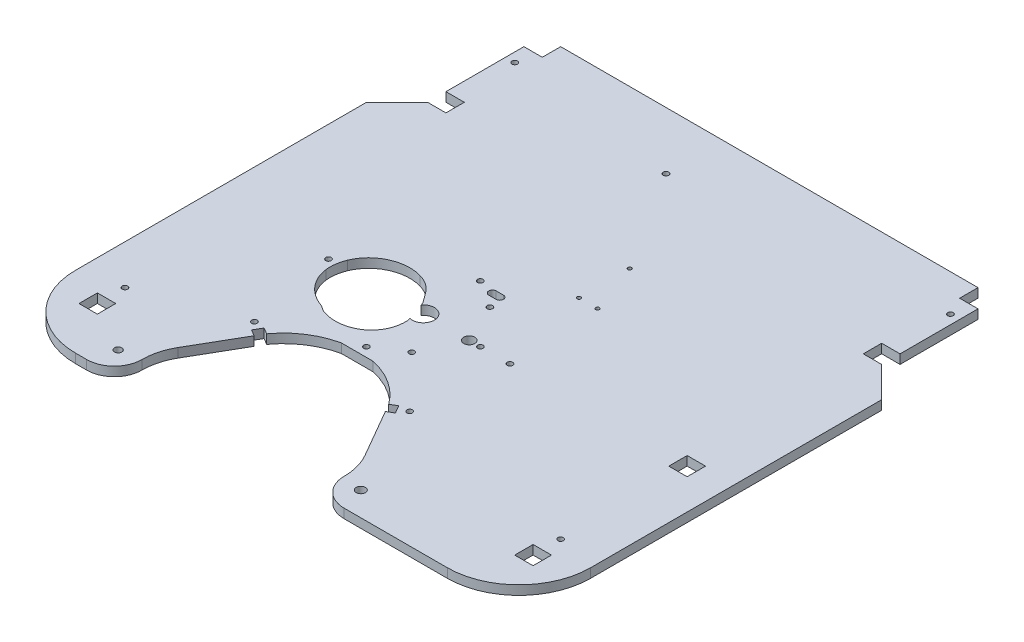
SolidWorks part; units mm, degrees
material "ABS PC"
ref_plane "Plan de face" through (0, 0, 0) normal (0, 0, 1) x (1, 0, 0)
ref_plane "Plan de dessus" through (0, 0, 0) normal (0, 1, 0) x (1, 0, 0)
ref_plane "Plan de droite" through (0, 0, 0) normal (1, 0, 0) x (0, 0, -1)
sketch "Esquisse1" plane through (0, 0, 0) normal (0, 1, 0) x (1, 0, 0)
  line L1 (-140.1, 31.2) -> (140.1, 31.2)
  line L2 (-140.1, 31.2) -> (-140.1, -245.0829)
  line L3 (-140.1, -245.0829) -> (140.1, -245.0829)
  line L4 (140.1, 31.2) -> (140.1, -245.0829)
  line L5 (45, -245.0829) -> (50, -245.0829) construction
  line L6 (-114.5, 31.2) -> (114.5, 31.2) construction
  line L7 (140.1, -4) -> (140.1, 4) construction
  line L8 (-140.1, 4) -> (-140.1, -4) construction
extrude "Boss.-Extru.1" add sketch "Esquisse1" along normal blind 5
sketch "Esquisse2" plane through (0, 0, 0) normal (0, 1, 0) x (1, 0, 0)
  line L3 (-58.1815, -184) -> (-61.6457, -182)
  line L4 (-61.6457, -182) -> (-64.1457, -186.3301)
  line L5 (-64.1457, -186.3301) -> (-60.6815, -188.3301)
  line L7 (-25, -132) -> (-25, -245.0829) construction
  line L8 (-58.1815, -184) -> (-60.6815, -188.3301) construction
  line L9 (-62.6323, -132) -> (62.6323, -132) construction
  line L10 (-25, -62.6323) -> (-25, 62.6323) construction
  line L11 (-60.6815, -188.3301) -> (-75.8539, -214.6094)
  line L13 (-58.1815, -184) -> (-54.7174, -186) construction
  line L14 (-25, -168.25) -> (-25, -231.25) construction
  line L16 (140.1, -245.0829) -> (-157.7205, -245.0829) construction
  line L17 (-140.1, -245.0829) -> (140.1, -245.0829) construction
  line L18 (8.1815, -184) -> (4.7174, -186) construction
  line L20 (8.1815, -184) -> (10.6815, -188.3301) construction
  line L21 (10.6815, -188.3301) -> (25.8539, -214.6094)
  line L22 (14.1457, -186.3301) -> (10.6815, -188.3301)
  line L23 (11.6457, -182) -> (14.1457, -186.3301)
  line L24 (8.1815, -184) -> (11.6457, -182)
  line L25 (-62.8957, -184.1651) -> (-67.2258, -181.6651) construction
  line L26 (-95, -245.0829) -> (45, -245.0829)
  arc A0 (-95, -245.0829) -> (-86.2863, -217.8734) centre (-95, -230.0829) ccw construction
  arc A1 (8.1815, -184) -> (-58.1815, -184) centre (-25, -208.0829) ccw
  arc A2 (-95, -245.0829) -> (-80, -230.0829) centre (-95, -230.0829) ccw
  arc A4 (-80, -230.0829) -> (-75.8539, -214.6094) centre (-49.0531, -230.0829) cw
  arc A5 (30, -230.0829) -> (25.8539, -214.6094) centre (-0.9469, -230.0829) ccw
  arc A6 (45, -245.0829) -> (30, -230.0829) centre (45, -230.0829) cw
  circle A8 centre (-67.2258, -181.6651) radius 1.5
  circle A10 centre (17.2258, -181.6651) radius 1.5
  dimension "D4" = 41
  dimension "D8" = 5
  dimension "D9" = 3
  dimension "D1" = 4
  dimension "D2" = 52
  dimension "D3" = 37
  dimension "D5" = 90
  dimension "D6" = 5
  dimension "D7" = 30
extrude "Enlèv. mat.-Extru.2" cut sketch "Esquisse2" along normal through all
sketch "Esquisse3" plane through (0, 5, 0) normal (0, 1, 0) x (1, 0, 0)
  line L0 (-30.2198, -127.0596) -> (-26.1089, -139.1328)
  spline S0 degree 3 poles (-37.7914, -122.1402) (-38.0734, -121.8243) (-38.3657, -121.5165) (-38.9965, -120.9381) (-39.3221, -120.6716) (-39.9982, -120.1678) (-40.3476, -119.9323) (-41.0674, -119.4915) (-41.4393, -119.2855) (-41.8168, -119.0963) knots 0 0 0 0 0.25 0.25 0.5 0.5 0.75 0.75 1 1 1 1 construction
  spline S1 degree 3 poles (-32.1541, -129.7487) (-32.3725, -129.4202) (-32.6019, -129.0988) (-33.0628, -128.4574) (-33.2929, -128.1364) (-33.9829, -127.1734) (-34.442, -126.5306) (-35.3645, -125.2486) (-35.8282, -124.6096) (-36.7788, -123.3501) (-37.2654, -122.7294) (-37.7914, -122.1402) knots 0 0 0 0 0.125 0.125 0.25 0.25 0.5 0.5 0.75 0.75 1 1 1 1 construction
  spline S2 degree 3 poles (-35.6619, -154.1946) (-35.0242, -153.7971) (-34.4156, -153.3543) (-33.5487, -152.619) (-33.2665, -152.3609) (-32.7231, -151.8244) (-32.4631, -151.5476) (-31.717, -150.6924) (-31.2669, -150.0877) (-30.6603, -149.1305) (-30.4697, -148.8029) (-30.1129, -148.13) (-29.9465, -147.7839) (-29.4899, -146.7378) (-29.243, -146.0234) (-28.8562, -144.563) (-28.7157, -143.8147) (-28.4532, -141.5381) (-28.491, -140.0256) (-28.7111, -138.5175) knots 0 0 0 0 0.125 0.125 0.1875 0.1875 0.25 0.25 0.375 0.375 0.4375 0.4375 0.5 0.5 0.625 0.625 0.75 0.75 1 1 1 1 construction
  spline S3 degree 3 poles (-35.6619, -154.1946) (-36.3253, -154.608) (-37.0218, -154.968) (-38.4509, -155.5833) (-39.1871, -155.8402) (-40.6929, -156.2533) (-41.4552, -156.4075) (-42.998, -156.615) (-43.7804, -156.6676) (-46.0993, -156.6733) (-47.6259, -156.4799) (-49.5088, -155.9804) (-49.8836, -155.8673) (-50.622, -155.6166) (-50.9867, -155.4786) (-51.7066, -155.1765) (-52.0616, -155.0123) (-52.5826, -154.748) (-52.7564, -154.66) (-53.0886, -154.4564) (-53.2465, -154.3401) (-53.4028, -154.2206) knots 0 0 0 0 0.125 0.125 0.25 0.25 0.375 0.375 0.5 0.5 0.75 0.75 0.8125 0.8125 0.875 0.875 0.9375 0.9375 0.96875 0.96875 1 1 1 1 construction
  spline S4 degree 3 poles (-41.8168, -119.0963) (-42.9717, -118.5173) (-44.1778, -118.0898) (-46.0518, -117.6406) (-46.691, -117.5235) (-47.9689, -117.3572) (-48.6085, -117.3074) (-49.8889, -117.2725) (-50.5296, -117.2869) (-51.8124, -117.3808) (-52.4575, -117.4608) (-54.3583, -117.7944) (-55.5875, -118.1406) (-57.3737, -118.8468) (-57.9613, -119.1147) (-59.1074, -119.714) (-59.6598, -120.0407) (-61.253, -121.1053) (-62.2339, -121.9217) (-63.3433, -123.0959) (-63.5595, -123.3389) (-63.9727, -123.8343) (-64.1705, -124.0875) (-64.7392, -124.8624) (-65.0859, -125.3992) (-65.725, -126.5066) (-66.0166, -127.0778) (-66.4118, -127.9607) (-66.5364, -128.2602) (-66.7677, -128.8619) (-66.8752, -129.1647) (-67.3727, -130.6881) (-67.6417, -131.9376) (-67.7975, -133.5423) (-67.8198, -133.8663) (-67.8456, -134.511) (-67.8492, -134.8322) (-67.832, -135.7928) (-67.7828, -136.429) (-67.6138, -137.6932) (-67.494, -138.3213) (-67.1803, -139.5691) (-66.9857, -140.1898) (-66.3106, -141.9951) (-65.7352, -143.1386) (-64.7029, -144.7728) (-64.3296, -145.3033) (-63.5406, -146.3156) (-63.1238, -146.8009) (-62.2475, -147.7313) (-61.7884, -148.177) (-60.8134, -149.015) (-60.2997, -149.4102) (-59.6532, -149.8941) (-59.524, -149.9912) (-59.2621, -150.18) (-59.1281, -150.2696) (-58.7233, -150.5349) (-58.4482, -150.704) (-57.6091, -151.1904) (-57.0301, -151.4842) (-56.1848, -151.9623) (-55.907, -152.1283) (-55.4954, -152.386) (-55.361, -152.4765) (-55.1045, -152.6783) (-54.9822, -152.7884) (-54.7446, -153.015) (-54.6281, -153.1308) (-54.3929, -153.36) (-54.2744, -153.4736) (-53.9142, -153.8089) (-53.6638, -154.0209) (-53.4028, -154.2206) knots 0 0 0 0 0.0625 0.0625 0.09375 0.09375 0.125 0.125 0.15625 0.15625 0.1875 0.1875 0.25 0.25 0.28125 0.28125 0.3125 0.3125 0.375 0.375 0.390625 0.390625 0.40625 0.40625 0.4375 0.4375 0.46875 0.46875 0.484375 0.484375 0.5 0.5 0.5625 0.5625 0.578125 0.578125 0.59375 0.59375 0.625 0.625 0.65625 0.65625 0.6875 0.6875 0.75 0.75 0.78125 0.78125 0.8125 0.8125 0.84375 0.84375 0.875 0.875 0.882813 0.882813 0.890625 0.890625 0.90625 0.90625 0.9375 0.9375 0.953125 0.953125 0.960938 0.960938 0.96875 0.96875 0.976563 0.976563 0.984375 0.984375 1 1 1 1 construction
  spline S30 degree 3 poles (-26.1089, -139.1328) (-25.957, -141.5638) (-26.2233, -144.068) (-26.9566, -146.3908) knots 0 0 0 0 1 1 1 1
  spline S31 degree 3 poles (-26.9566, -146.3908) (-27.2228, -147.2342) (-27.8831, -148.8893) (-29.2029, -151.171) (-30.8763, -153.2749) (-32.1537, -154.4712) (-32.834, -155.0244) knots 0 0 0 0 0.25 0.5 0.75 1 1 1 1
  spline S32 degree 3 poles (-32.834, -155.0244) (-34.0816, -156.0391) (-36.8741, -157.7375) (-39.9456, -158.6891) (-41.5144, -158.9883) knots 0 0 0 0 0.5 1 1 1 1
  spline S33 degree 3 poles (-41.5144, -158.9883) (-44.1178, -159.4848) (-46.8613, -159.4832) (-49.4654, -158.9908) knots 0 0 0 0 1 1 1 1
  spline S34 degree 3 poles (-49.4654, -158.9908) (-49.952, -158.8988) (-50.9201, -158.6805) (-51.9843, -158.3611) (-52.6895, -158.1153) (-53.0279, -157.9903) (-53.4112, -157.8436) (-53.8185, -157.6386) (-54.1411, -157.4539) (-54.4726, -157.2537) (-54.8017, -157.0368) (-54.9983, -156.9002) (-55.0989, -156.8301) knots 0 0 0 0 0.25 0.5 0.5625 0.625 0.6875 0.75 0.8125 0.875 0.9375 1 1 1 1
  spline S35 degree 3 poles (-55.0989, -156.8301) (-55.3218, -156.6748) (-55.8004, -156.3308) (-56.3372, -156.039) (-57.1153, -155.7047) (-58.1073, -155.2831) (-59.4212, -154.7248) (-60.6952, -154.0815) (-61.7162, -153.4751) (-62.6513, -152.8651) (-64.3061, -151.7169) (-66.4424, -149.811) (-68.6708, -147.1371) (-71.0288, -143.199) (-72.0496, -139.8117) (-72.3207, -137.531) knots 0 0 0 0 0.03125 0.0625 0.09375 0.125 0.1875 0.25 0.28125 0.3125 0.375 0.5 0.625 0.75 1 1 1 1
  spline S36 degree 3 poles (-72.3207, -137.531) (-72.524, -135.8208) (-72.4832, -132.3293) (-71.5647, -128.9796) (-70.9127, -127.3896) knots 0 0 0 0 0.5 1 1 1 1
  spline S37 degree 3 poles (-70.9127, -127.3896) (-70.401, -126.1419) (-69.1411, -123.7476) (-66.5657, -120.5334) (-63.4815, -117.9312) (-59.9208, -115.9009) (-56.1194, -114.5638) (-52.0895, -113.8994) (-48.0382, -113.9466) (-45.3685, -114.4522) (-44.0724, -114.8246) knots 0 0 0 0 0.125 0.25 0.375 0.5 0.625 0.75 0.875 1 1 1 1
  spline S38 degree 3 poles (-44.0724, -114.8246) (-43.1335, -115.0943) (-41.3015, -115.7539) (-39.094, -116.9388) (-37.4723, -118.0859) (-36.3006, -119.1013) (-35.2972, -120.193) (-34.6853, -120.94) (-34.3845, -121.3211) knots 0 0 0 0 0.25 0.5 0.625 0.75 0.875 1 1 1 1
  spline S39 degree 3 poles (-34.3845, -121.3211) (-33.6538, -122.2469) (-32.5988, -123.6857) (-31.2416, -125.568) (-30.5443, -126.5566) (-30.2198, -127.0596) knots 0 0 0 0 0.5 0.75 1 1 1 1
  spline S40 degree 3 poles (-544.0684, -2053.4709) (-13.3203, -329.9447) (2.5957, -129.3013) (-46.0518, -117.6406) (-46.691, -117.5235) (-47.9689, -117.3572) (-48.6085, -117.3074) (-49.8889, -117.2725) (-50.5296, -117.2869) (-51.8124, -117.3808) (-52.4575, -117.4608) (-54.3583, -117.7944) (-55.5875, -118.1406) (-57.3737, -118.8468) (-57.9613, -119.1147) (-59.1074, -119.714) (-59.6598, -120.0407) (-61.253, -121.1053) (-62.2339, -121.9217) (-63.3433, -123.0959) (-63.5595, -123.3389) (-63.9727, -123.8343) (-64.1705, -124.0875) (-64.7392, -124.8624) (-65.0859, -125.3992) (-65.725, -126.5066) (-66.0166, -127.0778) (-66.4118, -127.9607) (-66.5364, -128.2602) (-66.7677, -128.8619) (-66.8752, -129.1647) (-67.3727, -130.6881) (-67.6417, -131.9376) (-67.7975, -133.5423) (-67.8198, -133.8663) (-67.8456, -134.511) (-67.8492, -134.8322) (-67.832, -135.7928) (-67.7828, -136.429) (-67.6138, -137.6932) (-67.494, -138.3213) (-67.1803, -139.5691) (-66.9857, -140.1898) (-66.3106, -141.9951) (-65.7352, -143.1386) (-64.7029, -144.7728) (-64.3296, -145.3033) (-63.5406, -146.3156) (-63.1238, -146.8009) (-62.2475, -147.7313) (-61.7884, -148.177) (-60.8134, -149.015) (-60.2997, -149.4102) (-59.6532, -149.8941) (-59.524, -149.9912) (-59.2621, -150.18) (-59.1281, -150.2696) (-58.7233, -150.5349) (-58.4482, -150.704) (-57.6091, -151.1904) (-57.0301, -151.4842) (-56.1848, -151.9623) (-55.907, -152.1283) (-55.4954, -152.386) (-55.361, -152.4765) (-55.1045, -152.6783) (-54.9822, -152.7884) (-54.7446, -153.015) (-54.6281, -153.1308) (-54.3929, -153.36) (-54.2744, -153.4736) (-26.8241, -179.0197) (131.7308, -54.8381) (1346.14, 1273.1767) knots -2.339844 -2.339844 -2.339844 -2.339844 0.0625 0.0625 0.09375 0.09375 0.125 0.125 0.15625 0.15625 0.1875 0.1875 0.25 0.25 0.28125 0.28125 0.3125 0.3125 0.375 0.375 0.390625 0.390625 0.40625 0.40625 0.4375 0.4375 0.46875 0.46875 0.484375 0.484375 0.5 0.5 0.5625 0.5625 0.578125 0.578125 0.59375 0.59375 0.625 0.625 0.65625 0.65625 0.6875 0.6875 0.75 0.75 0.78125 0.78125 0.8125 0.8125 0.84375 0.84375 0.875 0.875 0.882813 0.882813 0.890625 0.890625 0.90625 0.90625 0.9375 0.9375 0.953125 0.953125 0.960938 0.960938 0.96875 0.96875 0.976563 0.976563 0.984375 0.984375 2.762304 2.762304 2.762304 2.762304 only from (-41.8168, -119.0963) to (-53.4028, -154.2206)
  spline S41 degree 3 poles (-1939.2427, 445.2377) (-11.3915, 5.3531) (-2.0926, -139.9279) (-38.4509, -155.5833) (-39.1871, -155.8402) (-40.6929, -156.2533) (-41.4552, -156.4075) (-42.998, -156.615) (-43.7804, -156.6676) (-46.0993, -156.6733) (-47.6259, -156.4799) (-49.5088, -155.9804) (-49.8836, -155.8673) (-50.622, -155.6166) (-50.9867, -155.4786) (-51.7066, -155.1765) (-52.0616, -155.0123) (-52.5826, -154.748) (-52.7564, -154.66) (-62.008, -148.9921) (-46.7728, -99.7044) (-1052.7685, -1886.2862) knots -6.110057 -6.110057 -6.110057 -6.110057 0.125 0.125 0.25 0.25 0.375 0.375 0.5 0.5 0.75 0.75 0.8125 0.8125 0.875 0.875 0.9375 0.9375 0.96875 0.96875 2.678123 2.678123 2.678123 2.678123 only from (-35.6619, -154.1946) to (-53.4028, -154.2206)
  spline S42 degree 3 poles (805.3246, -1958.3687) (-625.9447, 427.7737) (-104.0787, -212.4384) (-33.5487, -152.619) (-33.2665, -152.3609) (-32.7231, -151.8244) (-32.4631, -151.5476) (-31.717, -150.6924) (-31.2669, -150.0877) (-30.6603, -149.1305) (-30.4697, -148.8029) (-30.1129, -148.13) (-29.9465, -147.7839) (-29.4899, -146.7378) (-29.243, -146.0234) (-28.8562, -144.563) (-28.7157, -143.8147) (-20.1781, -69.7717) (-507.9815, -8.4894) (1948.7508, 124.0064) knots -15.067184 -15.067184 -15.067184 -15.067184 0.125 0.125 0.1875 0.1875 0.25 0.25 0.375 0.375 0.4375 0.4375 0.5 0.5 0.625 0.625 0.75 0.75 12.82174 12.82174 12.82174 12.82174 only from (-35.6619, -154.1946) to (-28.7111, -138.5175)
  spline S43 degree 3 poles (-1678.0425, -1265.3241) (-10.5484, -165.9011) (-20.1896, -146.3733) (-33.0628, -128.4574) (-33.2929, -128.1364) (-33.9829, -127.1734) (-34.442, -126.5306) (-35.3645, -125.2486) (-35.8282, -124.6096) (-54.2717, -100.1715) (-88.436, -89.3419) (-1650.9877, -1303.2795) knots -6.732601 -6.732601 -6.732601 -6.732601 0.125 0.125 0.25 0.25 0.5 0.5 0.75 0.75 10.201277 10.201277 10.201277 10.201277 only from (-32.1541, -129.7487) to (-37.7914, -122.1402)
  spline S44 degree 3 poles (1561.6634, 1077.8271) (-67.121, -199.6011) (-22.5068, -136.058) (-38.9965, -120.9381) (-39.3221, -120.6716) (-39.9982, -120.1678) (-40.3476, -119.9323) (-65.1031, -104.7717) (-144.7605, -156.1255) (1752.928, -999.5442) knots -12.570471 -12.570471 -12.570471 -12.570471 0.25 0.25 0.5 0.5 0.75 0.75 17.69557 17.69557 17.69557 17.69557 only from (-37.7914, -122.1402) to (-41.8168, -119.0963)
extrude "Enlèv. mat.-Extru.3" cut sketch "Esquisse3" against normal through all
sketch "Esquisse4" plane through (0, 5, 0) normal (0, 1, 0) x (1, 0, 0)
  circle A0 centre (19.9, -82.15) radius 1
  circle A1 centre (9.8, -82.15) radius 1
  circle A2 centre (9.8, -54.55) radius 1
  dimension "D1" = 2
extrude "Enlèv. mat.-Extru.4" cut sketch "Esquisse4" against normal through all
sketch "Esquisse5" plane through (0, 5, 0) normal (0, 1, 0) x (1, 0, 0)
  circle A0 centre (22.1224, -132) radius 1.5
  circle A1 centre (-10.0508, -153.25) radius 1.5
  circle A2 centre (-25, -163) radius 1.5
  circle A3 centre (-10.0508, -110.75) radius 1.5
  circle A4 centre (-25, -101) radius 1.5
  circle A5 centre (-76.6, -132) radius 1.5
  circle A6 centre (6, -132) radius 1.5 construction
  circle A7 centre (6, -132) radius 1.5
  circle A8 centre (0, -132) radius 3
  arc A9 (1.5616, -134.5616) -> (1.5616, -129.4384) centre (0, -132) ccw construction
  circle A10 centre (-10.0508, -110.75) radius 1.5 construction
  dimension "D1" = 3
extrude "Enlèv. mat.-Extru.5" cut sketch "Esquisse5" against normal through all
sketch "Esquisse6" plane through (0, 5, 0) normal (0, 1, 0) x (1, 0, 0)
  circle A0 centre (-25, -132) radius 6
  circle A1 centre (-25, -132) radius 5.4 construction
  dimension "D1" = 12
extrude "Enlèv. mat.-Extru.6" cut sketch "Esquisse6" against normal through all
sketch "Esquisse7" plane through (0, 5, 0) normal (0, 1, 0) x (1, 0, 0)
  line L1 (-16, -103.4) -> (-12, -103.4) construction
  line L2 (-16, -101.4) -> (-12, -101.4)
  line L3 (-16, -105.4) -> (-12, -105.4)
  arc A0 (-16, -101.4) -> (-16, -105.4) centre (-16, -103.4) ccw
  arc A6 (-12, -105.4) -> (-12, -101.4) centre (-12, -103.4) ccw
  arc A7 (-11.4091, -103.2958) -> (-12.5909, -103.2958) centre (-12, -103.4) ccw construction
  arc A9 (-15.4091, -103.2958) -> (-16.5909, -103.2958) centre (-16, -103.4) ccw construction
  point P2 (-14, -103.4)
  dimension "D1" = 4
extrude "Enlèv. mat.-Extru.7" cut sketch "Esquisse7" against normal through all
sketch "Esquisse8" plane through (0, 5, 0) normal (0, 1, 0) x (1, 0, 0)
  line L0 (140.1, -245.0829) -> (140.1, 31.2) construction
  line L1 (101.1, -245.0829) -> (140.1, -245.0829)
  line L2 (140.1, -245.0829) -> (140.1, -206.0829)
  line L3 (-140.1, -245.0829) -> (-140.1, -206.0829)
  line L4 (-140.1, 31.2) -> (-140.1, -245.0829) construction
  line L5 (-140.1, -245.0829) -> (-95, -245.0829) construction
  line L6 (-101.1, -245.0829) -> (-140.1, -245.0829)
  arc A0 (140.1, -206.0829) -> (101.1, -245.0829) centre (101.1, -206.0829) cw
  arc A1 (-140.1, -206.0829) -> (-101.1, -245.0829) centre (-101.1, -206.0829) ccw
extrude "Enlèv. mat.-Extru.8" cut sketch "Esquisse8" against normal through all
sketch "Esquisse9" plane through (0, 5, 0) normal (0, 1, 0) x (1, 0, 0)
  line L0 (-113.5, 21.2) -> (-123.5, 21.2) construction
  line L1 (-113.5, 21.2) -> (-113.5, 31.2) construction
  line L2 (-113.5, -31.2) -> (-113.5, -21.2) construction
  line L3 (-113.5, -21.2) -> (-123.5, -21.2) construction
  line L4 (-113.5, -31.2) -> (-123.5, -31.2) construction
  line L5 (-113.5, 21.2) -> (-123.5, 21.2)
  line L6 (-113.5, 21.2) -> (-113.5, 31.2)
  line L7 (-113.5, -31.2) -> (-113.5, -21.2)
  line L8 (-113.5, -21.2) -> (-123.5, -21.2)
  line L9 (-113.5, -31.2) -> (-123.5, -31.2)
  line L10 (-123.5, -21.2) -> (-123.5, 21.2)
  line L11 (-123.5, -31.2) -> (-140.1, -47.8)
  line L12 (-140.1, 31.2) -> (-140.1, -206.0829) construction
  line L13 (-140.1, -47.8) -> (-140.1, 31.2)
  line L14 (-140.1, 31.2) -> (-113.5, 31.2)
  line L15 (0, 0) -> (0, 79.4635) construction
  line L16 (140.1, 31.2) -> (113.5, 31.2)
  line L17 (140.1, -47.8) -> (140.1, 31.2)
  line L18 (123.5, -31.2) -> (140.1, -47.8)
  line L19 (123.5, -21.2) -> (123.5, 21.2)
  line L20 (113.5, -31.2) -> (123.5, -31.2)
  line L21 (113.5, -21.2) -> (123.5, -21.2)
  line L22 (113.5, -31.2) -> (113.5, -21.2)
  line L23 (113.5, 21.2) -> (113.5, 31.2)
  line L24 (113.5, 21.2) -> (123.5, 21.2)
  dimension "D1" = 45
extrude "Enlèv. mat.-Extru.9" cut sketch "Esquisse9" against normal through all
sketch "Esquisse10" plane through (0, 0, 0) normal (0, -1, 0) x (1, 0, 0)
  line L1 (-100, 245.0829) -> (-100, 242.0829) construction
  line L2 (-95, 242.0829) -> (-100, 242.0829) construction
  line L4 (45, 242.0829) -> (50, 242.0829) construction
  line L5 (50, 242.0829) -> (50, 245.0829)
  line L6 (50, 245.0829) -> (45, 245.0829)
  line L7 (45, 242.0829) -> (50, 242.0829)
  line L8 (50, 245.0829) -> (50, 242.0829) construction
  line L9 (-101.1, 245.0829) -> (-95, 245.0829) construction
  line L11 (45, 245.0829) -> (50, 245.0829) construction
  line L20 (-95, 245.0829) -> (-100, 245.0829)
  line L21 (-100, 245.0829) -> (-100, 242.0829)
  line L22 (-100, 242.0829) -> (-95, 242.0829)
  arc A0 (-88.029, 220.3153) -> (-25, 23.5) centre (-25, 132) ccw construction
  arc A1 (-86.2863, 217.8734) -> (-25, 26.5) centre (-25, 132) ccw construction
  arc A2 (-25, 26.5) -> (36.2863, 217.8734) centre (-25, 132) ccw construction
  arc A3 (-25, 23.5) -> (38.029, 220.3153) centre (-25, 132) ccw construction
  arc A4 (-88.029, 220.3153) -> (-25, 23.5) centre (-25, 132) ccw
  arc A5 (-86.2863, 217.8734) -> (-25, 26.5) centre (-25, 132) ccw
  arc A6 (-25, 26.5) -> (36.2863, 217.8734) centre (-25, 132) ccw
  arc A7 (-25, 23.5) -> (38.029, 220.3153) centre (-25, 132) ccw
  arc A8 (45, 245.0829) -> (36.2863, 217.8734) centre (45, 230.0829) ccw construction
  arc A10 (45, 245.0829) -> (36.2863, 217.8734) centre (45, 230.0829) ccw
  arc A11 (45, 242.0829) -> (38.029, 220.3153) centre (45, 230.0829) ccw
  arc A12 (45, 242.0829) -> (38.029, 220.3153) centre (45, 230.0829) ccw construction
  arc A14 (-88.029, 220.3153) -> (-95, 242.0829) centre (-95, 230.0829) ccw construction
  arc A15 (-80, 230.0829) -> (-95, 245.0829) centre (-95, 230.0829) ccw construction
  arc A16 (-86.2863, 217.8734) -> (-95, 245.0829) centre (-95, 230.0829) ccw
  arc A17 (-88.029, 220.3153) -> (-95, 242.0829) centre (-95, 230.0829) ccw
extrude "Enlèv. mat.-Extru.10" [suppressed] cut sketch "Esquisse10" against normal blind 1
sketch "Esquisse11" plane through (0, 5, 0) normal (0, 1, 0) x (1, 0, 0)
  line L4 (-123.5, -210.8) -> (-123.5, -220.8)
  line L5 (-113.5, -210.8) -> (-123.5, -210.8)
  line L6 (-113.5, -220.8) -> (-113.5, -210.8)
  line L7 (-123.5, -220.8) -> (-113.5, -220.8)
  line L8 (-123.5, -210.8) -> (-123.5, -220.8)
  line L9 (-113.5, -210.8) -> (-123.5, -210.8)
  line L10 (-113.5, -220.8) -> (-113.5, -210.8)
  line L11 (-123.5, -220.8) -> (-113.5, -220.8)
  line L12 (113.5, -210.8) -> (113.5, -220.8)
  line L13 (123.5, -210.8) -> (113.5, -210.8)
  line L14 (123.5, -220.8) -> (123.5, -210.8)
  line L15 (113.5, -220.8) -> (123.5, -220.8)
  line L16 (113.5, -210.8) -> (113.5, -220.8)
  line L17 (123.5, -210.8) -> (113.5, -210.8)
  line L18 (123.5, -220.8) -> (123.5, -210.8)
  line L19 (113.5, -220.8) -> (123.5, -220.8)
  line L20 (123.5, -137) -> (123.5, -127)
  line L21 (113.5, -137) -> (123.5, -137)
  line L22 (113.5, -127) -> (113.5, -137)
  line L23 (123.5, -127) -> (113.5, -127)
  line L24 (123.5, -137) -> (123.5, -127)
  line L25 (113.5, -137) -> (123.5, -137)
  line L26 (113.5, -127) -> (113.5, -137)
  line L27 (123.5, -127) -> (113.5, -127)
  dimension "D1" = 0
  dimension "D2" = 0
  dimension "D3" = 0
extrude "Enlèv. mat.-Extru.11" cut sketch "Esquisse11" against normal through all
sketch "Esquisse12" plane through (0, 5, 0) normal (0, 1, 0) x (1, 0, 0)
  circle A0 centre (41, -232) radius 2.5 construction
  circle A1 centre (41, -232) radius 2.5
  circle A2 centre (-91, -232) radius 2 construction
  circle A3 centre (-91, -232) radius 2
extrude "Enlèv. mat.-Extru.12" cut sketch "Esquisse12" against normal through all
sketch "Esquisse13" plane through (0, 5, 0) normal (0, 1, 0) x (1, 0, 0)
  circle A0 centre (-118.5, -200.8) radius 1.5
  circle A1 centre (-118.5, 11.2) radius 1.5
  circle A2 centre (-118.5, 11.2) radius 1.525 construction
  circle A3 centre (-118.5, -200.8) radius 1.525 construction
  circle A4 centre (118.5, 11.2) radius 1.5
  circle A5 centre (118.5, -200.8) radius 1.5
  circle A6 centre (118.5, -200.8) radius 1.25 construction
  circle A7 centre (-25, 0) radius 1.5
  circle A9 centre (-25, 0) radius 1.5 construction
  dimension "D1" = 3
extrude "Enlèv. mat.-Extru.15" cut sketch "Esquisse13" against normal through all
sketch "Esquisse14" plane through (0, 0, 0) normal (0, -1, 0) x (1, 0, 0)
  line L0 (-115.5, 168) -> (115.5, 168) construction
  line L1 (-33.6234, 168) -> (-16.3766, 168)
  line L2 (-33.6234, 168) -> (-33.6234, 166)
  line L3 (-33.6234, 166) -> (-16.3766, 166)
  line L4 (-16.3766, 168) -> (-16.3766, 166)
  arc A0 (-58.1815, 184) -> (8.1815, 184) centre (-25, 208.0829) ccw construction
  dimension "D1" = 17.2468
  dimension "D2" = 2
extrude "Boss.-Extru.2" add sketch "Esquisse14" against normal up to surface (5 mm away) up to face at (-25, 5, 1.5)
